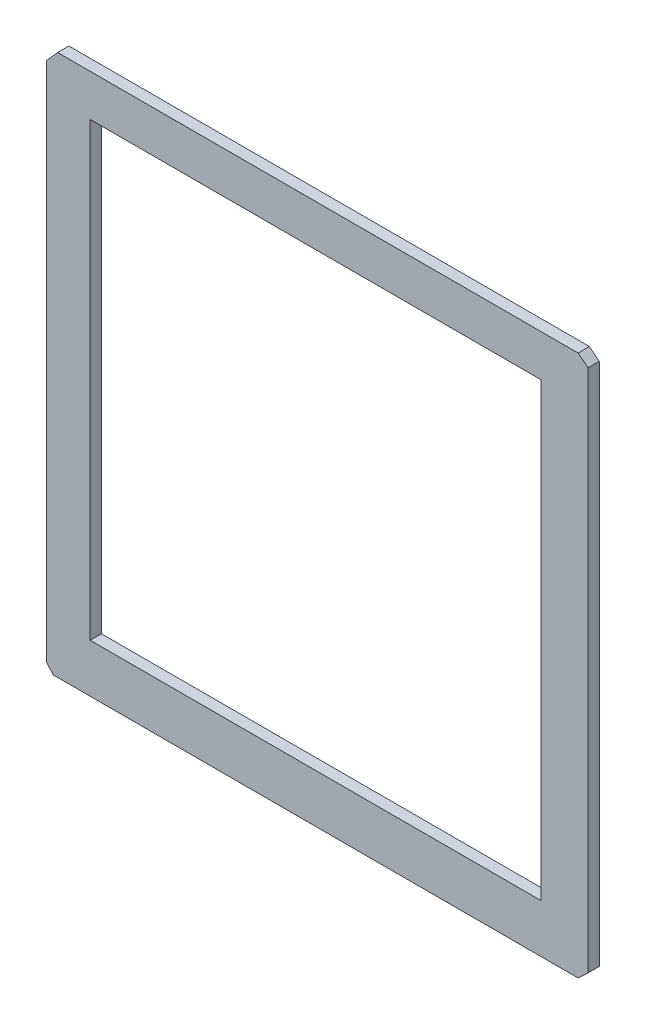
SolidWorks part; units mm, degrees
ref_plane "Alzado" through (0, 0, 0) normal (0, 0, 1) x (1, 0, 0)
ref_plane "Planta" through (0, 0, 0) normal (0, 1, 0) x (1, 0, 0)
ref_plane "Vista lateral" through (0, 0, 0) normal (1, 0, 0) x (0, 0, -1)
sketch "Croquis1" plane through (0, 0, 0) normal (0, 0, 1) x (1, 0, 0)
  line L0 (-52.2938, 34.4074) -> (-12.2938, 34.4074)
  line L1 (-12.2938, 34.4074) -> (-12.2938, -5.5926)
  line L2 (-12.2938, -5.5926) -> (-52.2938, -5.5926)
  line L3 (-52.2938, -5.5926) -> (-52.2938, 34.4074)
  line L4 (-55.1791, 38.1068) -> (-9.021, 38.1068)
  line L5 (-8.146, 37.4043) -> (-8.146, -9.068)
  line L6 (-9.021, -9.8932) -> (-55.575, -9.8932)
  line L7 (-56.146, -9.2233) -> (-56.146, 37.0232)
  line L8 (-9.021, 38.1068) -> (-8.146, 37.4043)
  line L9 (-8.146, -9.068) -> (-9.021, -9.8932)
  line L10 (-56.146, -9.2233) -> (-55.575, -9.8932)
  line L11 (-55.1791, 38.1068) -> (-56.146, 37.0232)
  dimension "D1" = 40
  dimension "D2" = 40
  dimension "D3" = 48
  dimension "D4" = 48
extrude "Saliente-Extruir1" add sketch "Croquis1" along normal blind 1
